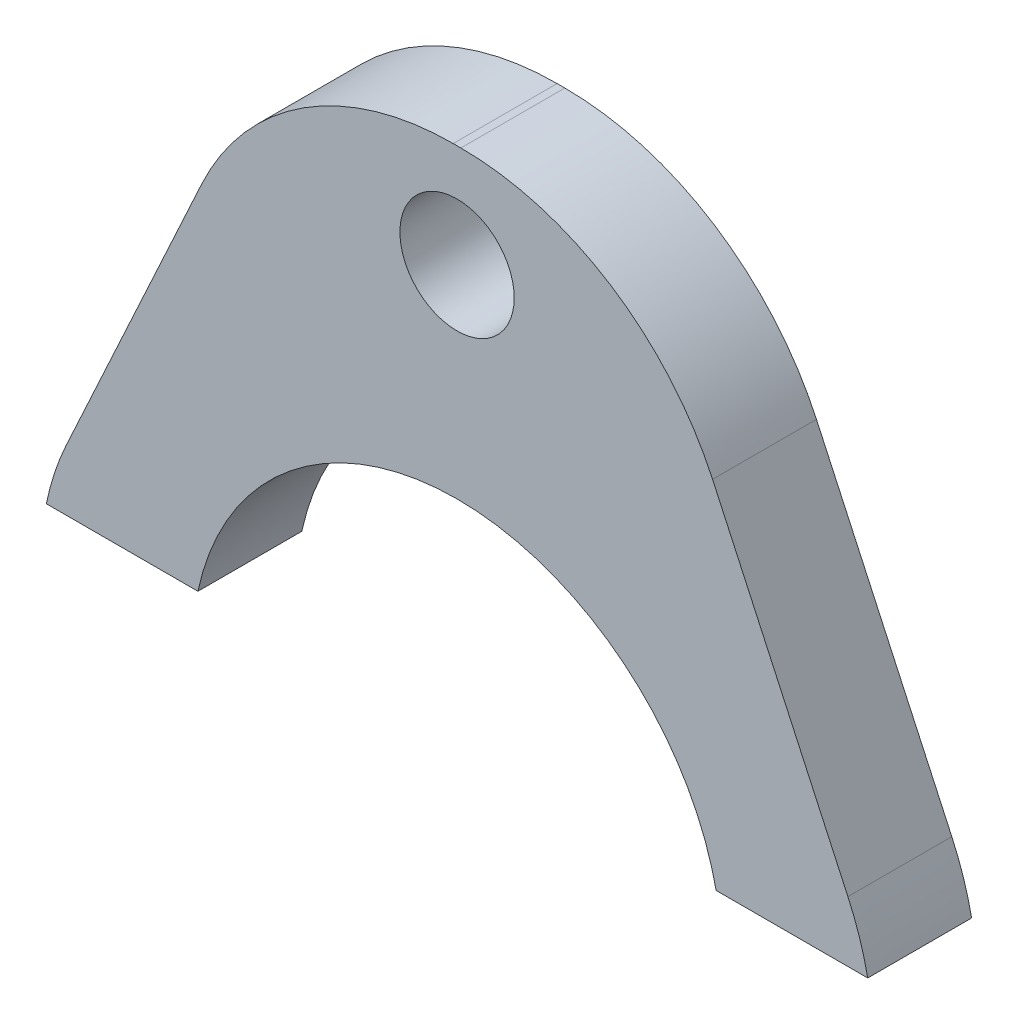
SolidWorks part; units mm, degrees
ref_plane "Plano frontal" through (0, 0, 0) normal (0, 0, 1) x (1, 0, 0)
ref_plane "Plano superior" through (0, 0, 0) normal (0, 1, 0) x (1, 0, 0)
ref_plane "Plano direito" through (0, 0, 0) normal (1, 0, 0) x (0, 0, -1)
sketch "Esboço1" plane through (0, 0, 0) normal (0, 0, 1) x (1, 0, 0)
  line L0 (0, -13.5) -> (0, 13.5) construction
  line L3 (0, 0) -> (7.65, 0) construction
  line L6 (-11.2846, 3.3481) -> (-5.2332, 16.48)
  line L8 (-5.2332, 16.48) -> (5.2332, 16.48)
  line L9 (11.2846, 3.3481) -> (5.2332, 16.48)
  line L10 (11.2846, -3.3481) -> (5.2332, -16.48) construction
  line L11 (-5.2332, -16.48) -> (5.2332, -16.48) construction
  line L12 (-11.2846, -3.3481) -> (-5.2332, -16.48) construction
  line L13 (0, 0) -> (-10.5806, -4.8757) construction
  line L14 (-12.0901, 1.6) -> (12.0901, 1.6)
  circle A1 centre (0, 0) radius 7.65
  circle A2 centre (0, -13.5) radius 1.65 construction
  circle A3 centre (0, 13.5) radius 1.65
  circle A4 centre (0, 13.5) radius 3 construction
  circle A5 centre (0, -13.5) radius 3 construction
  circle A6 centre (0, 0) radius 17.48 construction
  arc A7 (11.2846, 3.3481) -> (11.2846, -3.3481) centre (4.0189, 0) cw
  arc A8 (-11.2846, 3.3481) -> (-11.2846, -3.3481) centre (-4.0189, 0) ccw
  point P8 (0, 11.85)
  point P10 (0, 7.65)
  point P11 (0, 10.5)
  point P13 (-6.9478, -3.2017)
  point P22 (0, 16.48)
  point P24 (0, 17.48)
  point P28 (12.8275, 0)
  point P31 (-12.8275, 0)
  point P35 (0, -20.7406)
  dimension "D1" = 3.3
  dimension "D2" = 15.3
  dimension "D4" = 6
  dimension "D5" = 6
  dimension "D6" = 4
  dimension "D7" = 34.96
  dimension "D8" = 1
  dimension "D10" = 8
  dimension "D3" = 27
  dimension "D9" = 1.6
extrude "Ressalto-extrusão1" add sketch "Esboço1" along normal blind 3 contours A1 L14 L9 L8 L6 A3
fillet "Filete1" radius 8 2 edges at (-5.2332, 16.48, 1.5) (5.2332, 16.48, 1.5)
